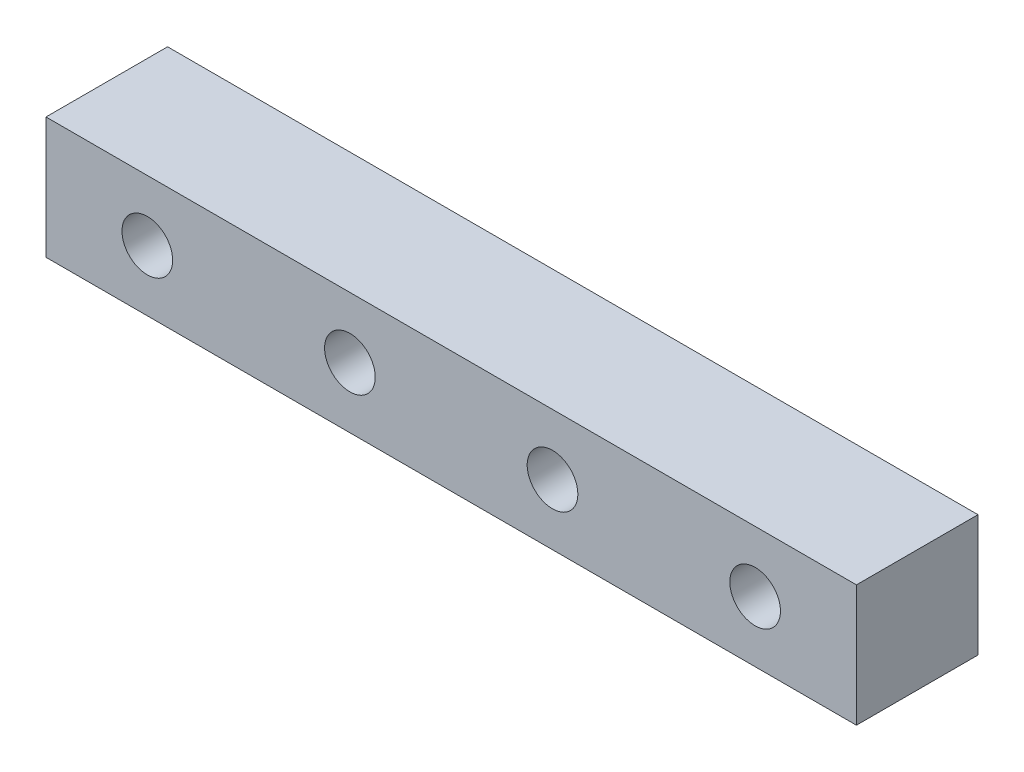
SolidWorks part; units mm, degrees
material "6061-T6 (SS)"
ref_plane "前视基准面" through (0, 0, 0) normal (0, 0, 1) x (1, 0, 0)
ref_plane "上视基准面" through (0, 0, 0) normal (0, 1, 0) x (1, 0, 0)
ref_plane "右视基准面" through (0, 0, 0) normal (1, 0, 0) x (0, 0, -1)
sketch "草图1" plane through (0, 0, 0) normal (0, 0, 1) x (1, 0, 0)
  line L0 (0, 0) -> (10, 0) construction
  line L2 (35, 3) -> (-5, 3)
  line L3 (35, 3) -> (35, -3)
  line L4 (35, -3) -> (-5, -3)
  line L5 (-5, 3) -> (-5, -3)
  line L6 (35, 3) -> (-5, -3) construction
  line L7 (35, -3) -> (-5, 3) construction
  circle A0 centre (0, 0) radius 1.25
  circle A1 centre (10, 0) radius 1.25
  circle A2 centre (20, 0) radius 1.25
  circle A3 centre (30, 0) radius 1.25
  point P3 (15, 0)
  dimension "D3" = 2.5
  dimension "D6" = 5
  dimension "D2" = 10
  dimension "D4" = 6
  dimension "D5" = 5
  dimension "D1" = 4
extrude "凸台-拉伸1" add sketch "草图1" along normal blind 6
cosmetic thread "装饰螺纹线1" parameters "D2"=3
cosmetic thread "装饰螺纹线2" parameters "D2"=3
cosmetic thread "装饰螺纹线3" parameters "D2"=3
cosmetic thread "装饰螺纹线4" parameters "D2"=3
